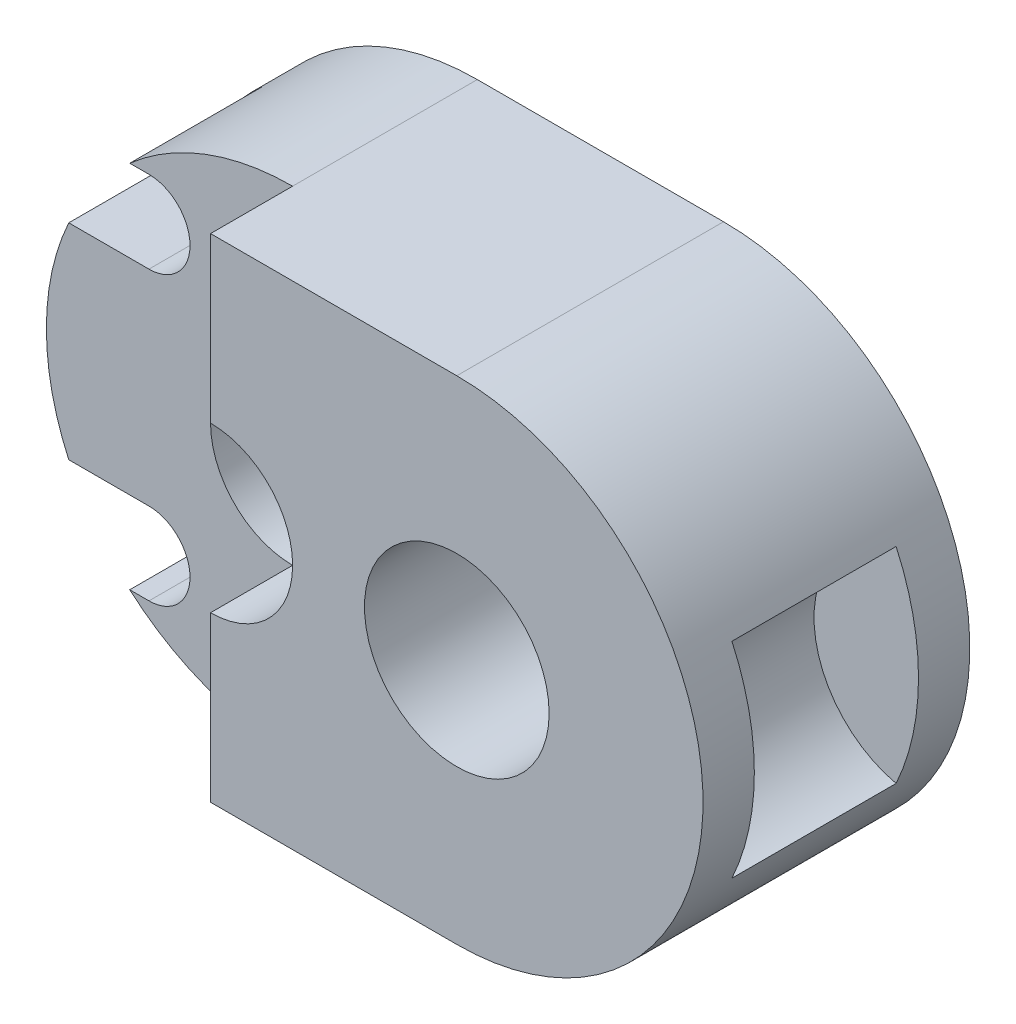
SolidWorks part; units mm, degrees
ref_plane "Front" through (0, 0, 0) normal (0, 0, 1) x (1, 0, 0)
ref_plane "Top" through (0, 0, 0) normal (0, 1, 0) x (1, 0, 0)
ref_plane "Right" through (0, 0, 0) normal (1, 0, 0) x (0, 0, -1)
sketch "Sketch1" plane through (0, 0, 0) normal (0, 0, 1) x (1, 0, 0)
  line L0 (-3, 0) -> (3, 0) construction
  line L1 (-3, 6) -> (3, 6)
  line L2 (-3, -6) -> (3, -6)
  arc A0 (-3, 6) -> (-3, -6) centre (-3, 0) ccw
  arc A1 (3, -6) -> (3, 6) centre (3, 0) ccw
  circle A2 centre (-3, 0) radius 0.5
  point P3 (0, 0)
  dimension "D3" = 6
  dimension "D1" = 6
  dimension "D2" = 0
extrude "Boss-Extrude1" add sketch "Sketch1" along normal mid plane 6.5
sketch "Sketch2" plane through (0, 0, 0) normal (0, 0, 1) x (1, 0, 0)
  line L0 (3, 6) -> (-3, 6) construction
  line L1 (-3, -6) -> (3, -6) construction
  arc A0 (8.4544, 2.5) -> (8.4544, -2.5) centre (9.0169, 0) ccw
  arc A1 (3, -6) -> (3, 6) centre (3, 0) ccw construction
  arc A3 (8.4544, 2.5) -> (8.4544, -2.5) centre (3, 0) cw
  point P10 (6.4544, 0)
  dimension "D3" = 2
  dimension "D1" = 3.5
  dimension "D2" = 3.5
extrude "Cut-Extrude1" cut sketch "Sketch2" against normal mid plane 4
sketch "Sketch3" plane through (0, 0, 3.25) normal (0, 0, 1) x (1, 0, 0)
  line L1 (-3, 6) -> (-12.7097, 6)
  line L2 (-3, 6) -> (-3, -7.0558)
  line L3 (-3, -7.0558) -> (-12.7097, -7.0558)
  line L4 (-12.7097, 6) -> (-12.7097, -7.0558)
extrude "Cut-Extrude2" cut sketch "Sketch3" against normal blind 2
sketch "Sketch4" plane through (0, 0, 3.25) normal (0, 0, 1) x (1, 0, 0)
  arc A3 (-3, 2) -> (-3, -2) centre (-3, 0) ccw
  arc A4 (-3, -2) -> (-3, 2) centre (-3, 0) ccw
  arc A5 (-3, -2) -> (-3, 2) centre (-3, 0) ccw
  dimension "D1" = 1.5
extrude "Cut-Extrude3" cut sketch "Sketch4" against normal blind 3.5
sketch "Sketch5" plane through (0, 0, 3.25) normal (0, 0, 1) x (1, 0, 0)
  circle A0 centre (3, 0) radius 2.25
  dimension "D1" = 4.5
extrude "Cut-Extrude4" cut sketch "Sketch5" against normal blind 3.5
sketch "Sketch6" plane through (0, 0, 1.25) normal (0, 0, 1) x (1, 0, 0)
  line L0 (-6.5, 3.5) -> (-10.1117, 3.5) construction
  line L1 (0.5, -3.5) -> (-6.5, -3.5)
  line L2 (0.5, -3.5) -> (0.5, 3.5)
  line L3 (0.5, 3.5) -> (-6.5, 3.5)
  line L4 (-6.5, -3.5) -> (-6.5, 3.5)
  line L5 (0.5, -3.5) -> (-6.5, 3.5) construction
  line L6 (0.5, 3.5) -> (-6.5, -3.5) construction
  line L7 (-6.5, 2.5) -> (-10.1117, 2.5)
  line L8 (-6.5, 4.5) -> (-10.1117, 4.5)
  line L9 (-6.5, -3.5) -> (-10.1117, -3.5) construction
  line L10 (-6.5, -4.5) -> (-10.1117, -4.5)
  line L11 (-6.5, -2.5) -> (-10.1117, -2.5)
  arc A0 (-6.5, 2.5) -> (-6.5, 4.5) centre (-6.5, 3.5) ccw
  arc A1 (-10.1117, 4.5) -> (-10.1117, 2.5) centre (-10.1117, 3.5) ccw
  arc A2 (-6.5, -4.5) -> (-6.5, -2.5) centre (-6.5, -3.5) ccw
  arc A3 (-10.1117, -2.5) -> (-10.1117, -4.5) centre (-10.1117, -3.5) ccw
  point P0 (-3, 0)
  point P6 (-8.3058, 3.5)
  point P12 (-8.3058, -3.5)
  arc M7 (-3, 6) -> (-3, -6) centre (-3, 0) ccw
  dimension "D4" = 1
  dimension "D5" = 1
  dimension "D1" = 7
  dimension "D2" = 7
  dimension "D3" = 3.6117
extrude "Cut-Extrude5" cut sketch "Sketch6" against normal blind 3.25 contours L8 A1 L7 M7 | L3 A0 L8 L7 L4 M7 | L4 A0 L3 | L10 A2 L1 L4 L11 M7 | L11 A3 L10 M7
hole_wizard "M1.2x0.25 Tapped Hole1" positions "3DSketch2" profile "Sketch7" tap size "M1.2x0.25" standard "ISO"
sketch3d "3DSketch2"
  line L0 (3, 0, -0.25) -> (3, 0, 3.25) construction
  line L1 (-6.5, 3.5, -2) -> (-6.5, 3.5, 1.25) construction
  line L2 (-6.5, -3.5, -2) -> (-6.5, -3.5, 1.25) construction
  point P0 (3, 0, -0.25)
  point P4 (-6.5, 3.5, -2)
  point P8 (-6.5, -3.5, -2)
sketch "Sketch7" plane through (3, 0, -0.25) normal (1, 0, 0) x (0, -1, 0)
  line L0 (0, 0) -> (0, 13.9354)
  line L1 (0, 13.9354) -> (0.475, 13.65)
  line L2 (0.475, 13.65) -> (0.475, 0)
  line L5 (0.475, 0) -> (0, 0)
  line L10 (0, 13.9354) -> (-0.475, 13.65) construction
  line L11 (0, -6.35) -> (0, 107.95) construction
  dimension "Tap Drill Dia." = 0.95
  dimension "Tap Drill Depth" = 13.65
  dimension "Drill Angle" = 118
cosmetic thread "Hole Thread1" parameters "D1"=1.25, "D2"=1.2
cosmetic thread "Hole Thread2" parameters "D1"=1.25, "D2"=1.2
cosmetic thread "Hole Thread3" parameters "D1"=2.5, "D2"=1.2
sketch "Sketch8" plane through (0, 0, 0) normal (0, 1, 0) x (1, 0, 0)
  line L0 (2.5204, 0.25) -> (2.525, 3.25)
  line L1 (0.75, 0.25) -> (5.25, 0.25) construction
  line L2 (3.475, 3.25) -> (2.525, 3.25) construction
  line L3 (3, 3.25) -> (-3, 3.25) construction
